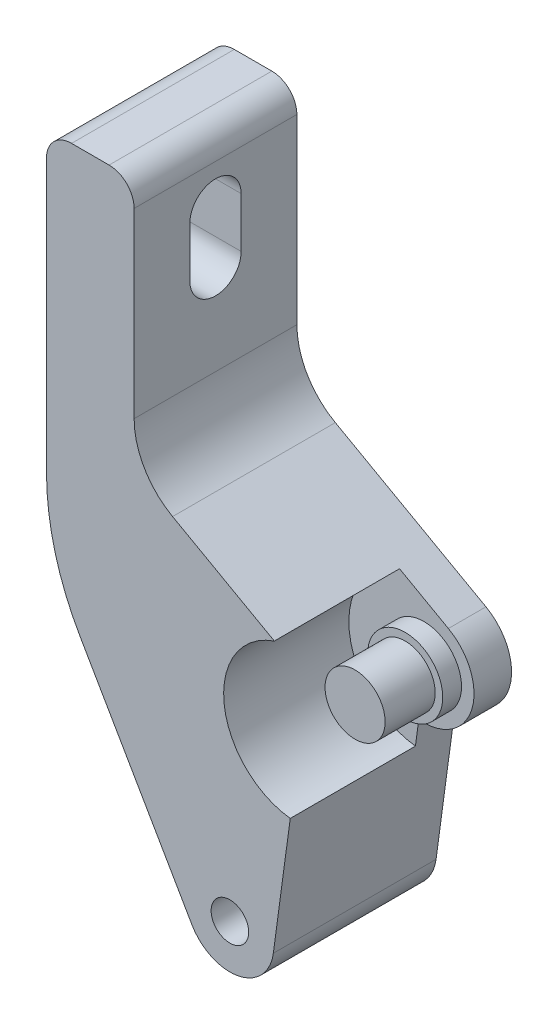
SolidWorks part; units mm, degrees
ref_plane "Front Plane" through (0, 0, 0) normal (0, 0, 1) x (1, 0, 0)
ref_plane "Top Plane" through (0, 0, 0) normal (0, 1, 0) x (1, 0, 0)
ref_plane "Right Plane" through (0, 0, 0) normal (1, 0, 0) x (0, 0, -1)
sketch "Sketch1" plane through (0, 0, 0) normal (0, 0, 1) x (1, 0, 0)
  line L0 (-12.0315, -15.9684) -> (-10.4125, -3.9787)
  line L1 (-9.25, -5.9529) -> (-11.5977, -16.3787) construction
  line L2 (-18.5311, -17.25) -> (-30.15, 2.8745)
  line L3 (-30.15, 2.8745) -> (-30.15, 32)
  line L4 (-0.431, 32) -> (-12.15, 32) construction
  line L5 (-30.15, 32) -> (-23.15, 32)
  line L6 (-23.15, 32) -> (-23.15, 15.4561)
  line L7 (-21.15, -11.5) -> (-21.15, 15.4561) construction
  line L8 (-20.0786, 10.2193) -> (-8.0476, 3.4912)
  line L9 (-29.15, -19.5) -> (-21.15, -19.5) construction
  circle A1 centre (-15.5, -15.5) radius 1.5
  arc A2 (-18.5311, -17.25) -> (-12.0315, -15.9684) centre (-15.5, -15.5) ccw
  arc A3 (-10.4125, -3.9787) -> (-8.0476, 3.4912) centre (-10, 0) ccw
  arc A4 (-9.25, -5.9529) -> (-4.5781, -2.5697) centre (-10, 0) ccw construction
  arc A5 (-23.15, 15.4561) -> (-20.0786, 10.2193) centre (-17.15, 15.4561) ccw
  circle A6 centre (-15.5, -15.5) radius 1.5 construction
  arc A9 (-21.15, 15.4561) -> (-16.9371, 11.4617) centre (-17.15, 15.4561) ccw construction
  dimension "D1" = 7
  dimension "D2" = 8
  dimension "D3" = 5
  dimension "D4" = 2
  dimension "D5" = 7
  dimension "D6" = 60
extrude "Boss-Extrude1" add sketch "Sketch1" along normal blind 3
sketch "Sketch2" plane through (0, 0, 3) normal (0, 0, 1) x (1, 0, 0)
  circle A0 centre (-10, 0) radius 3
  arc A1 (-10.4125, -3.9787) -> (-8.0476, 3.4912) centre (-10, 0) ccw construction
  dimension "D1" = 6
extrude "Boss-Extrude2" add sketch "Sketch2" along normal offset from surface (1.5 mm away) 2
sketch "Sketch3" plane through (0, 0, 4.5) normal (0, 0, 1) x (1, 0, 0)
  circle A0 centre (-10, 0) radius 2.4
  dimension "D1" = 4.8
extrude "Boss-Extrude3" add sketch "Sketch3" along normal offset from surface (4 mm away) 2
sketch "Sketch4" plane through (0, 0, 3) normal (0, 0, 1) x (1, 0, 0)
  line L6 (-12.0315, -15.9684) -> (-10.4125, -3.9787)
  line L7 (-8.0476, 3.4912) -> (-20.0786, 10.2193)
  line L8 (-23.15, 15.4561) -> (-23.15, 32)
  line L9 (-23.15, 32) -> (-30.15, 32)
  line L10 (-30.15, 32) -> (-30.15, 2.8745)
  line L11 (-30.15, 2.8745) -> (-18.5311, -17.25)
  line L12 (-12.0315, -15.9684) -> (-10.6802, -5.9613)
  line L13 (-11.9508, 5.674) -> (-20.0786, 10.2193)
  line L14 (-23.15, 15.4561) -> (-23.15, 32)
  line L15 (-23.15, 32) -> (-30.15, 32)
  line L16 (-30.15, 32) -> (-30.15, 2.8745)
  line L17 (-30.15, 2.8745) -> (-18.5311, -17.25)
  arc A0 (-11.9508, 5.674) -> (-10.6802, -5.9613) centre (-10, 0) ccw
  circle A1 centre (-10, 0) radius 3 construction
  circle A2 centre (-15.5, -15.5) radius 1.5 construction
  circle A3 centre (-15.5, -15.5) radius 1.5
  arc A5 (-18.5311, -17.25) -> (-12.0315, -15.9684) centre (-15.5, -15.5) ccw
  arc A6 (-10.4125, -3.9787) -> (-8.0476, 3.4912) centre (-10, 0) ccw
  arc A7 (-23.15, 15.4561) -> (-20.0786, 10.2193) centre (-17.15, 15.4561) ccw
  arc A8 (-18.5311, -17.25) -> (-12.0315, -15.9684) centre (-15.5, -15.5) ccw
  arc A10 (-23.15, 15.4561) -> (-20.0786, 10.2193) centre (-17.15, 15.4561) ccw
  dimension "D1" = 12
  dimension "D2" = 0
extrude "Boss-Extrude4" add sketch "Sketch4" along normal offset from surface (10 mm away) 6
fillet "Fillet1" radius 20 1 edges at (-30.15, 2.8745, 6.5)
fillet "Fillet2" radius 2 2 edges at (-23.15, 32, 6.5) (-30.15, 32, 6.5)
sketch "Sketch5" plane through (-30.15, 0, 0) normal (-1, 0, 0) x (0, 0, 1)
  line L0 (6.5, 30) -> (6.5, 19.5) construction
  line L1 (6.5, 26.75) -> (6.5, 22.75) construction
  line L2 (8.55, 26.75) -> (8.55, 22.75)
  line L3 (4.45, 26.75) -> (4.45, 22.75)
  line L4 (13, 30) -> (0, 30) construction
  circle A0 centre (6.5, 24.75) radius 2.05 construction
  circle A1 centre (6.5, 24.75) radius 2.05 construction
  arc A2 (8.55, 26.75) -> (4.45, 26.75) centre (6.5, 26.75) ccw
  arc A3 (4.45, 22.75) -> (8.55, 22.75) centre (6.5, 22.75) ccw
  point P7 (6.5, 24.75)
  dimension "D1" = 4
extrude "Cut-Extrude1" cut sketch "Sketch5" against normal through all
mirror "Mirror1" [suppressed] about plane through (0, 0, 0) normal (1, 0, 0)
delete or keep bodies "Body-Delete1" [suppressed] type delete bodies bodies 105
